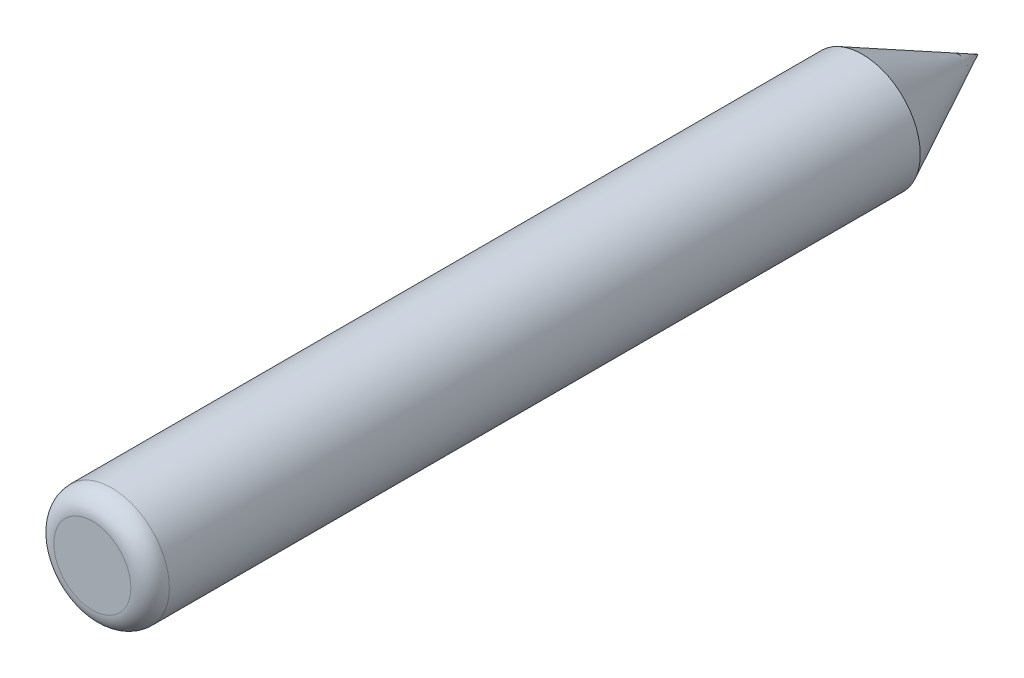
SolidWorks part; units mm, degrees
ref_plane "Plan de face" through (0, 0, 0) normal (0, 0, 1) x (1, 0, 0)
ref_plane "Plan de dessus" through (0, 0, 0) normal (0, 1, 0) x (1, 0, 0)
ref_plane "Plan de droite" through (0, 0, 0) normal (1, 0, 0) x (0, 0, -1)
sketch "Esquisse1" plane through (0, 0, 0) normal (0, 0, 1) x (1, 0, 0)
  circle A0 centre (0, 0) radius 6
  dimension "D1" = 12
extrude "Boss.-Extru.1" add sketch "Esquisse1" along normal blind 80
sketch "Esquisse4" plane through (0, 0, 0) normal (0, 1, 0) x (1, 0, 0)
  line L0 (0, 0) -> (0, 12)
  line L1 (0, 12) -> (-6, 0)
  line L2 (-6, 0) -> (0, 0)
  dimension "D1" = 12
revolve "Révolution1" add sketch "Esquisse4" angle 360 about L0
fillet "Congé1" radius 2 1 edges at (6, 0, 80)
